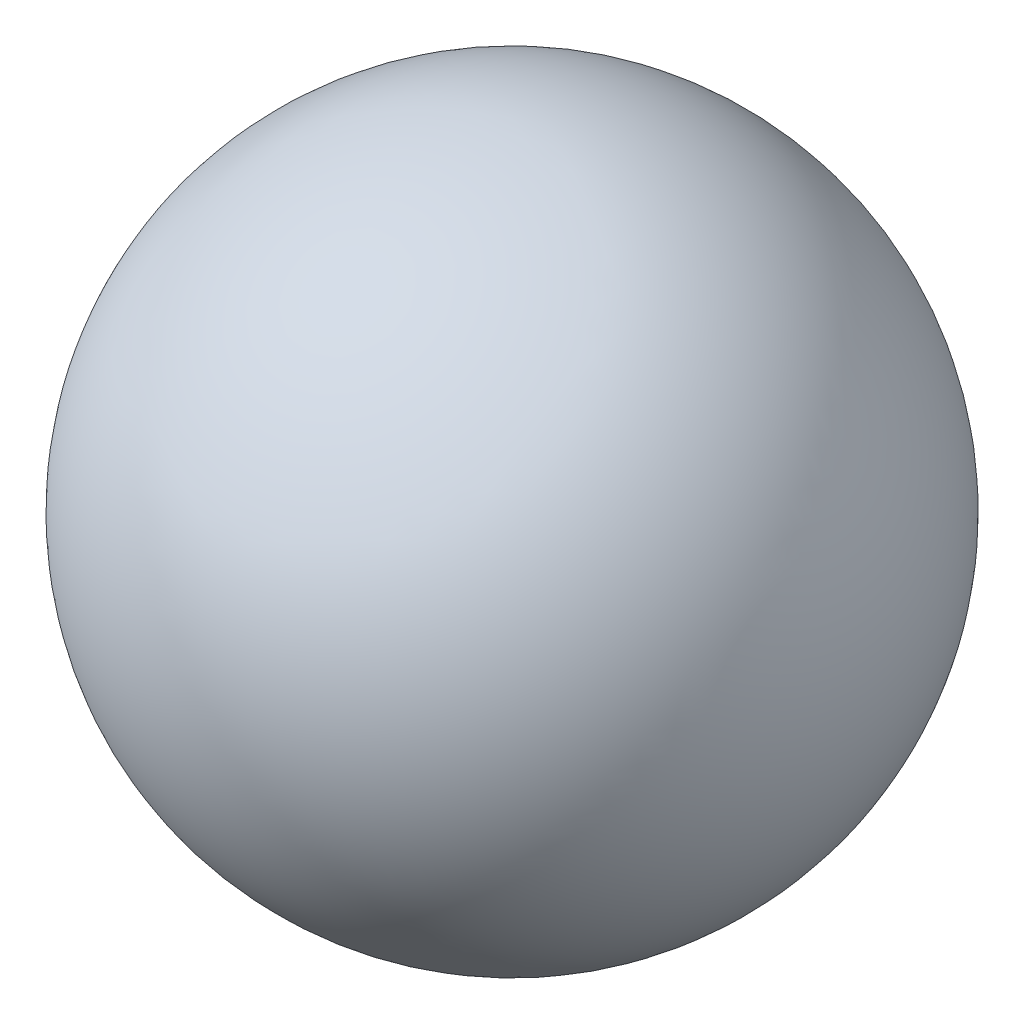
SolidWorks part; units mm, degrees
material "AISI Type 316L stainless steel"
ref_plane "Front Plane" through (0, 0, 0) normal (0, 0, 1) x (1, 0, 0)
ref_plane "Top Plane" through (0, 0, 0) normal (0, 1, 0) x (1, 0, 0)
ref_plane "Right Plane" through (0, 0, 0) normal (1, 0, 0) x (0, 0, -1)
ref_plane "Plane1" through (0, 0, 0) normal (0, 0, 1) x (1, 0, 0)
sketch "Sketch1" plane through (0, 0, 0) normal (0, 0, 1) x (1, 0, 0)
  line L0 (3.6905, 9.75) -> (1.3095, 9.75)
  line L1 (3.6905, 9.75) -> (1.3095, 9.75) construction
  arc A0 (1.3095, 9.75) -> (3.6905, 9.75) centre (2.5, 9.75) cw
revolve "Revolve1" add sketch "Sketch1" angle 360 about L1
other "Freeze***"
